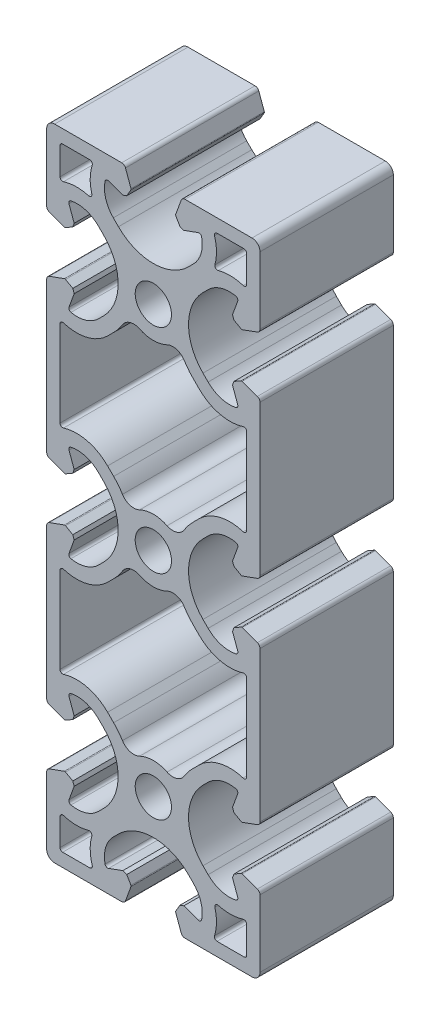
SolidWorks part; units mm, degrees
material "6005-T5"
ref_plane "Front" through (0, 0, 0) normal (0, 0, 1) x (1, 0, 0)
ref_plane "Top" through (0, 0, 0) normal (0, 1, 0) x (1, 0, 0)
ref_plane "Right" through (0, 0, 0) normal (1, 0, 0) x (0, 0, -1)
sketch "Sk Main Extrusion" plane through (0, 0, 0) normal (0, 0, 1) x (1, 0, 0)
  line L124 (17.5, 51.9407) -> (17.5, 57)
  line L125 (17, 57.5) -> (11.9407, 57.5)
  line L126 (-17.5, 57) -> (-17.5, 51.9407)
  line L127 (-11.9407, 57.5) -> (-17, 57.5)
  line L128 (-17.5, -51.9407) -> (-17.5, -57)
  line L129 (-17, -57.5) -> (-11.9407, -57.5)
  line L130 (11.9407, -57.5) -> (17, -57.5)
  line L131 (17.5, -57) -> (17.5, -51.9407)
  line L132 (17.5, 11.9407) -> (17.5, 28.0593)
  line L133 (8.5773, 30.5557) -> (7.4415, 31.6915)
  line L134 (-7.4415, 31.6915) -> (-8.5773, 30.5557)
  line L135 (-17.5, 28.0593) -> (-17.5, 11.9407)
  line L136 (-8.5773, 9.4443) -> (-7.4415, 8.3085)
  line L137 (7.4415, 8.3085) -> (8.5773, 9.4443)
  line L138 (-7.4415, -8.3085) -> (-8.5773, -9.4443)
  line L139 (-17.5, -11.9407) -> (-17.5, -28.0593)
  line L140 (-8.5773, -30.5557) -> (-7.4415, -31.6915)
  line L141 (7.4415, -31.6915) -> (8.5773, -30.5557)
  line L142 (17.5, -28.0593) -> (17.5, -11.9407)
  line L143 (8.5773, -9.4443) -> (7.4415, -8.3085)
  line L144 (4.1901, -56.6712) -> (5.2221, -59.5065)
  line L145 (5.9268, -60) -> (18.5, -60)
  line L146 (20, -58.5) -> (20, -45.9268)
  line L147 (19.5065, -45.2221) -> (16.6712, -44.1901)
  line L148 (16.4607, -44.2085) -> (15.1113, -44.9876)
  line L149 (15.1113, -44.9876) -> (14.8453, -45.7185)
  line L150 (14.8453, -45.7185) -> (15.8198, -48.3962)
  line L151 (10.2727, -47.5042) -> (9.3093, -46.5407)
  line L152 (9.3093, -33.4593) -> (10.2727, -32.4958)
  line L153 (15.8198, -31.6038) -> (14.8453, -34.2815)
  line L154 (14.8453, -34.2815) -> (15.1113, -35.0124)
  line L155 (15.1113, -35.0124) -> (16.4607, -35.7915)
  line L156 (16.6712, -35.8099) -> (19.5065, -34.7779)
  line L157 (20, -34.0732) -> (20, -5.9268)
  line L158 (19.5065, -5.2221) -> (16.6712, -4.1901)
  line L159 (16.4607, -4.2085) -> (15.1113, -4.9876)
  line L160 (15.1113, -4.9876) -> (14.8453, -5.7185)
  line L161 (14.8453, -5.7185) -> (15.8198, -8.3962)
  line L162 (10.2727, -7.5042) -> (9.3093, -6.5407)
  line L163 (9.3093, 6.5407) -> (10.2727, 7.5042)
  line L164 (15.8198, 8.3962) -> (14.8453, 5.7185)
  line L165 (14.8453, 5.7185) -> (15.1113, 4.9876)
  line L166 (15.1113, 4.9876) -> (16.4607, 4.2085)
  line L167 (16.6712, 4.1901) -> (19.5065, 5.2221)
  line L168 (20, 5.9268) -> (20, 34.0732)
  line L169 (19.5065, 34.7779) -> (16.6712, 35.8099)
  line L170 (16.4607, 35.7915) -> (15.1113, 35.0124)
  line L171 (15.1113, 35.0124) -> (14.8453, 34.2815)
  line L172 (14.8453, 34.2815) -> (15.8198, 31.6038)
  line L173 (10.2727, 32.4958) -> (9.3093, 33.4593)
  line L174 (9.3093, 46.5407) -> (10.2727, 47.5042)
  line L175 (15.8198, 48.3962) -> (14.8453, 45.7185)
  line L176 (14.8453, 45.7185) -> (15.1113, 44.9876)
  line L177 (15.1113, 44.9876) -> (16.4607, 44.2085)
  line L178 (16.6712, 44.1901) -> (19.5065, 45.2221)
  line L179 (20, 45.9268) -> (20, 58.5)
  line L180 (18.5, 60) -> (5.9268, 60)
  line L181 (5.2221, 59.5065) -> (4.1901, 56.6712)
  line L182 (4.2085, 56.4607) -> (4.9876, 55.1113)
  line L183 (4.9876, 55.1113) -> (5.7185, 54.8453)
  line L184 (5.7185, 54.8453) -> (8.3962, 55.8198)
  line L185 (7.5042, 50.2727) -> (6.5407, 49.3093)
  line L186 (-6.5407, 49.3093) -> (-7.5042, 50.2727)
  line L187 (-8.3962, 55.8198) -> (-5.7185, 54.8453)
  line L188 (-5.7185, 54.8453) -> (-4.9876, 55.1113)
  line L189 (-4.9876, 55.1113) -> (-4.2085, 56.4607)
  line L190 (-4.1901, 56.6712) -> (-5.2221, 59.5065)
  line L191 (-5.9268, 60) -> (-18.5, 60)
  line L192 (-20, 58.5) -> (-20, 45.9268)
  line L193 (-19.5065, 45.2221) -> (-16.6712, 44.1901)
  line L194 (-16.4607, 44.2085) -> (-15.1113, 44.9876)
  line L195 (-15.1113, 44.9876) -> (-14.8453, 45.7185)
  line L196 (-14.8453, 45.7185) -> (-15.8198, 48.3962)
  line L197 (-10.2727, 47.5042) -> (-9.3093, 46.5407)
  line L198 (-9.3093, 33.4593) -> (-10.2727, 32.4958)
  line L199 (-15.8198, 31.6038) -> (-14.8453, 34.2815)
  line L200 (-14.8453, 34.2815) -> (-15.1113, 35.0124)
  line L201 (-15.1113, 35.0124) -> (-16.4607, 35.7915)
  line L202 (-16.6712, 35.8099) -> (-19.5065, 34.7779)
  line L203 (-20, 34.0732) -> (-20, 5.9268)
  line L204 (-19.5065, 5.2221) -> (-16.6712, 4.1901)
  line L205 (-16.4607, 4.2085) -> (-15.1113, 4.9876)
  line L206 (-15.1113, 4.9876) -> (-14.8453, 5.7185)
  line L207 (-14.8453, 5.7185) -> (-15.8198, 8.3962)
  line L208 (-10.2727, 7.5042) -> (-9.3093, 6.5407)
  line L209 (-9.3093, -6.5407) -> (-10.2727, -7.5042)
  line L210 (-15.8198, -8.3962) -> (-14.8453, -5.7185)
  line L211 (-14.8453, -5.7185) -> (-15.1113, -4.9876)
  line L212 (-15.1113, -4.9876) -> (-16.4607, -4.2085)
  line L213 (-16.6712, -4.1901) -> (-19.5065, -5.2221)
  line L214 (-20, -5.9268) -> (-20, -34.0732)
  line L215 (-19.5065, -34.7779) -> (-16.6712, -35.8099)
  line L216 (-16.4607, -35.7915) -> (-15.1113, -35.0124)
  line L217 (-15.1113, -35.0124) -> (-14.8453, -34.2815)
  line L218 (-14.8453, -34.2815) -> (-15.8198, -31.6038)
  line L219 (-10.2727, -32.4958) -> (-9.3093, -33.4593)
  line L220 (-9.3093, -46.5407) -> (-10.2727, -47.5042)
  line L221 (-15.8198, -48.3962) -> (-14.8453, -45.7185)
  line L222 (-14.8453, -45.7185) -> (-15.1113, -44.9876)
  line L223 (-15.1113, -44.9876) -> (-16.4607, -44.2085)
  line L224 (-16.6712, -44.1901) -> (-19.5065, -45.2221)
  line L225 (-20, -45.9268) -> (-20, -58.5)
  line L226 (-18.5, -60) -> (-5.9268, -60)
  line L227 (-5.2221, -59.5065) -> (-4.1901, -56.6712)
  line L228 (-4.2085, -56.4607) -> (-4.9876, -55.1113)
  line L229 (-4.9876, -55.1113) -> (-5.7185, -54.8453)
  line L230 (-5.7185, -54.8453) -> (-8.3962, -55.8198)
  line L231 (-7.5042, -50.2727) -> (-6.5407, -49.3093)
  line L232 (6.5407, -49.3093) -> (7.5042, -50.2727)
  line L233 (8.3962, -55.8198) -> (5.7185, -54.8453)
  line L234 (5.7185, -54.8453) -> (4.9876, -55.1113)
  line L235 (4.9876, -55.1113) -> (4.2085, -56.4607)
  circle A139 centre (0, -40) radius 3.4
  circle A140 centre (0, 0) radius 3.4
  circle A141 centre (0, 40) radius 3.4
  arc A142 (11.9407, 57.5) -> (11.464, 56.8492) centre (11.9407, 57) ccw
  arc A143 (11.5401, 52.1568) -> (11.464, 56.8492) centre (3.646, 54.3755) ccw
  arc A144 (11.5401, 52.1568) -> (12.1568, 51.5401) centre (12.0215, 52.0215) ccw
  arc A145 (16.8492, 51.464) -> (12.1568, 51.5401) centre (14.3755, 43.646) ccw
  arc A146 (16.8492, 51.464) -> (17.5, 51.9407) centre (17, 51.9407) ccw
  arc A147 (17.5, 57) -> (17, 57.5) centre (17, 57) ccw
  arc A148 (-17, 57.5) -> (-17.5, 57) centre (-17, 57) ccw
  arc A149 (-17.5, 51.9407) -> (-16.8492, 51.464) centre (-17, 51.9407) ccw
  arc A150 (-12.1568, 51.5401) -> (-16.8492, 51.464) centre (-14.3755, 43.646) ccw
  arc A151 (-12.1568, 51.5401) -> (-11.5401, 52.1568) centre (-12.0215, 52.0215) ccw
  arc A152 (-11.464, 56.8492) -> (-11.5401, 52.1568) centre (-3.646, 54.3755) ccw
  arc A153 (-11.464, 56.8492) -> (-11.9407, 57.5) centre (-11.9407, 57) ccw
  arc A154 (-16.8492, -51.464) -> (-17.5, -51.9407) centre (-17, -51.9407) ccw
  arc A155 (-17.5, -57) -> (-17, -57.5) centre (-17, -57) ccw
  arc A156 (-11.9407, -57.5) -> (-11.464, -56.8492) centre (-11.9407, -57) ccw
  arc A157 (-11.5401, -52.1568) -> (-11.464, -56.8492) centre (-3.646, -54.3755) ccw
  arc A158 (-11.5401, -52.1568) -> (-12.1568, -51.5401) centre (-12.0215, -52.0215) ccw
  arc A159 (-16.8492, -51.464) -> (-12.1568, -51.5401) centre (-14.3755, -43.646) ccw
  arc A160 (12.1568, -51.5401) -> (11.5401, -52.1568) centre (12.0215, -52.0215) ccw
  arc A161 (11.464, -56.8492) -> (11.5401, -52.1568) centre (3.646, -54.3755) ccw
  arc A162 (11.464, -56.8492) -> (11.9407, -57.5) centre (11.9407, -57) ccw
  arc A163 (17, -57.5) -> (17.5, -57) centre (17, -57) ccw
  arc A164 (17.5, -51.9407) -> (16.8492, -51.464) centre (17, -51.9407) ccw
  arc A165 (12.1568, -51.5401) -> (16.8492, -51.464) centre (14.3755, -43.646) ccw
  arc A166 (16.8492, 11.464) -> (8.5773, 9.4443) centre (14.3755, 3.646) ccw
  arc A167 (16.8492, 11.464) -> (17.5, 11.9407) centre (17, 11.9407) ccw
  arc A168 (17.5, 28.0593) -> (16.8492, 28.536) centre (17, 28.0593) ccw
  arc A169 (8.5773, 30.5557) -> (16.8492, 28.536) centre (14.3755, 36.354) ccw
  arc A170 (5.2221, -59.5065) -> (5.9268, -60) centre (5.9268, -59.25) ccw
  arc A171 (18.5, -60) -> (20, -58.5) centre (18.5, -58.5) ccw
  arc A172 (20, -45.9268) -> (19.5065, -45.2221) centre (19.25, -45.9268) ccw
  arc A173 (16.6712, -44.1901) -> (16.4607, -44.2085) centre (16.5857, -44.425) ccw
  arc A174 (15.4507, -49.057) -> (15.8198, -48.3962) centre (15.35, -48.5672) ccw
  arc A175 (10.2727, -47.5042) -> (15.4507, -49.057) centre (14.3032, -43.4737) ccw
  arc A176 (9.3093, -33.4593) -> (9.3093, -46.5407) centre (15.85, -40) ccw
  arc A177 (15.4507, -30.943) -> (10.2727, -32.4958) centre (14.3032, -36.5263) ccw
  arc A178 (15.8198, -31.6038) -> (15.4507, -30.943) centre (15.35, -31.4328) ccw
  arc A179 (16.4607, -35.7915) -> (16.6712, -35.8099) centre (16.5857, -35.575) ccw
  arc A180 (19.5065, -34.7779) -> (20, -34.0732) centre (19.25, -34.0732) ccw
  arc A181 (20, -5.9268) -> (19.5065, -5.2221) centre (19.25, -5.9268) ccw
  arc A182 (16.6712, -4.1901) -> (16.4607, -4.2085) centre (16.5857, -4.425) ccw
  arc A183 (15.4507, -9.057) -> (15.8198, -8.3962) centre (15.35, -8.5672) ccw
  arc A184 (10.2727, -7.5042) -> (15.4507, -9.057) centre (14.3032, -3.4737) ccw
  arc A185 (9.3093, 6.5407) -> (9.3093, -6.5407) centre (15.85, 0) ccw
  arc A186 (15.4507, 9.057) -> (10.2727, 7.5042) centre (14.3032, 3.4737) ccw
  arc A187 (15.8198, 8.3962) -> (15.4507, 9.057) centre (15.35, 8.5672) ccw
  arc A188 (16.4607, 4.2085) -> (16.6712, 4.1901) centre (16.5857, 4.425) ccw
  arc A189 (19.5065, 5.2221) -> (20, 5.9268) centre (19.25, 5.9268) ccw
  arc A190 (20, 34.0732) -> (19.5065, 34.7779) centre (19.25, 34.0732) ccw
  arc A191 (16.6712, 35.8099) -> (16.4607, 35.7915) centre (16.5857, 35.575) ccw
  arc A192 (15.4507, 30.943) -> (15.8198, 31.6038) centre (15.35, 31.4328) ccw
  arc A193 (10.2727, 32.4958) -> (15.4507, 30.943) centre (14.3032, 36.5263) ccw
  arc A194 (9.3093, 46.5407) -> (9.3093, 33.4593) centre (15.85, 40) ccw
  arc A195 (15.4507, 49.057) -> (10.2727, 47.5042) centre (14.3032, 43.4737) ccw
  arc A196 (15.8198, 48.3962) -> (15.4507, 49.057) centre (15.35, 48.5672) ccw
  arc A197 (16.4607, 44.2085) -> (16.6712, 44.1901) centre (16.5857, 44.425) ccw
  arc A198 (19.5065, 45.2221) -> (20, 45.9268) centre (19.25, 45.9268) ccw
  arc A199 (20, 58.5) -> (18.5, 60) centre (18.5, 58.5) ccw
  arc A200 (5.9268, 60) -> (5.2221, 59.5065) centre (5.9268, 59.25) ccw
  arc A201 (4.1901, 56.6712) -> (4.2085, 56.4607) centre (4.425, 56.5857) ccw
  arc A202 (9.057, 55.4507) -> (8.3962, 55.8198) centre (8.5672, 55.35) ccw
  arc A203 (7.5042, 50.2727) -> (9.057, 55.4507) centre (3.4737, 54.3032) ccw
  arc A204 (-6.5407, 49.3093) -> (6.5407, 49.3093) centre (0, 55.85) ccw
  arc A205 (-9.057, 55.4507) -> (-7.5042, 50.2727) centre (-3.4737, 54.3032) ccw
  arc A206 (-8.3962, 55.8198) -> (-9.057, 55.4507) centre (-8.5672, 55.35) ccw
  arc A207 (-4.2085, 56.4607) -> (-4.1901, 56.6712) centre (-4.425, 56.5857) ccw
  arc A208 (-5.2221, 59.5065) -> (-5.9268, 60) centre (-5.9268, 59.25) ccw
  arc A209 (-18.5, 60) -> (-20, 58.5) centre (-18.5, 58.5) ccw
  arc A210 (-20, 45.9268) -> (-19.5065, 45.2221) centre (-19.25, 45.9268) ccw
  arc A211 (-16.6712, 44.1901) -> (-16.4607, 44.2085) centre (-16.5857, 44.425) ccw
  arc A212 (-15.4507, 49.057) -> (-15.8198, 48.3962) centre (-15.35, 48.5672) ccw
  arc A213 (-10.2727, 47.5042) -> (-15.4507, 49.057) centre (-14.3032, 43.4737) ccw
  arc A214 (-9.3093, 33.4593) -> (-9.3093, 46.5407) centre (-15.85, 40) ccw
  arc A215 (-15.4507, 30.943) -> (-10.2727, 32.4958) centre (-14.3032, 36.5263) ccw
  arc A216 (-15.8198, 31.6038) -> (-15.4507, 30.943) centre (-15.35, 31.4328) ccw
  arc A217 (-16.4607, 35.7915) -> (-16.6712, 35.8099) centre (-16.5857, 35.575) ccw
  arc A218 (-19.5065, 34.7779) -> (-20, 34.0732) centre (-19.25, 34.0732) ccw
  arc A219 (-20, 5.9268) -> (-19.5065, 5.2221) centre (-19.25, 5.9268) ccw
  arc A220 (-16.6712, 4.1901) -> (-16.4607, 4.2085) centre (-16.5857, 4.425) ccw
  arc A221 (-15.4507, 9.057) -> (-15.8198, 8.3962) centre (-15.35, 8.5672) ccw
  arc A222 (-10.2727, 7.5042) -> (-15.4507, 9.057) centre (-14.3032, 3.4737) ccw
  arc A223 (-9.3093, -6.5407) -> (-9.3093, 6.5407) centre (-15.85, 0) ccw
  arc A224 (-15.4507, -9.057) -> (-10.2727, -7.5042) centre (-14.3032, -3.4737) ccw
  arc A225 (-15.8198, -8.3962) -> (-15.4507, -9.057) centre (-15.35, -8.5672) ccw
  arc A226 (-16.4607, -4.2085) -> (-16.6712, -4.1901) centre (-16.5857, -4.425) ccw
  arc A227 (-19.5065, -5.2221) -> (-20, -5.9268) centre (-19.25, -5.9268) ccw
  arc A228 (-20, -34.0732) -> (-19.5065, -34.7779) centre (-19.25, -34.0732) ccw
  arc A229 (-16.6712, -35.8099) -> (-16.4607, -35.7915) centre (-16.5857, -35.575) ccw
  arc A230 (-15.4507, -30.943) -> (-15.8198, -31.6038) centre (-15.35, -31.4328) ccw
  arc A231 (-10.2727, -32.4958) -> (-15.4507, -30.943) centre (-14.3032, -36.5263) ccw
  arc A232 (-9.3093, -46.5407) -> (-9.3093, -33.4593) centre (-15.85, -40) ccw
  arc A233 (-15.4507, -49.057) -> (-10.2727, -47.5042) centre (-14.3032, -43.4737) ccw
  arc A234 (-15.8198, -48.3962) -> (-15.4507, -49.057) centre (-15.35, -48.5672) ccw
  arc A235 (-16.4607, -44.2085) -> (-16.6712, -44.1901) centre (-16.5857, -44.425) ccw
  arc A236 (-19.5065, -45.2221) -> (-20, -45.9268) centre (-19.25, -45.9268) ccw
  arc A237 (-20, -58.5) -> (-18.5, -60) centre (-18.5, -58.5) ccw
  arc A238 (-5.9268, -60) -> (-5.2221, -59.5065) centre (-5.9268, -59.25) ccw
  arc A239 (-4.1901, -56.6712) -> (-4.2085, -56.4607) centre (-4.425, -56.5857) ccw
  arc A240 (-9.057, -55.4507) -> (-8.3962, -55.8198) centre (-8.5672, -55.35) ccw
  arc A241 (-7.5042, -50.2727) -> (-9.057, -55.4507) centre (-3.4737, -54.3032) ccw
  arc A242 (6.5407, -49.3093) -> (-6.5407, -49.3093) centre (0, -55.85) ccw
  arc A243 (9.057, -55.4507) -> (7.5042, -50.2727) centre (3.4737, -54.3032) ccw
  arc A244 (8.3962, -55.8198) -> (9.057, -55.4507) centre (8.5672, -55.35) ccw
  arc A245 (4.2085, -56.4607) -> (4.1901, -56.6712) centre (4.425, -56.5857) ccw
  arc A246 (5.7881, 33.7692) -> (7.4415, 31.6915) centre (15.75, 40) ccw
  arc A247 (5.7881, 33.7692) -> (2.5767, 34.6924) centre (3.6686, 32.4434) ccw
  arc A248 (-2.5767, 34.6924) -> (2.5767, 34.6924) centre (0, 40) ccw
  arc A249 (-2.5767, 34.6924) -> (-5.7881, 33.7692) centre (-3.6686, 32.4434) ccw
  arc A250 (-7.4415, 31.6915) -> (-5.7881, 33.7692) centre (-15.75, 40) ccw
  arc A251 (-16.8492, 28.536) -> (-8.5773, 30.5557) centre (-14.3755, 36.354) ccw
  arc A252 (-16.8492, 28.536) -> (-17.5, 28.0593) centre (-17, 28.0593) ccw
  arc A253 (-17.5, 11.9407) -> (-16.8492, 11.464) centre (-17, 11.9407) ccw
  arc A254 (-8.5773, 9.4443) -> (-16.8492, 11.464) centre (-14.3755, 3.646) ccw
  arc A255 (-5.7881, 6.2308) -> (-7.4415, 8.3085) centre (-15.75, 0) ccw
  arc A256 (-5.7881, 6.2308) -> (-2.5767, 5.3076) centre (-3.6686, 7.5566) ccw
  arc A257 (2.5767, 5.3076) -> (-2.5767, 5.3076) centre (0, 0) ccw
  arc A258 (2.5767, 5.3076) -> (5.7881, 6.2308) centre (3.6686, 7.5566) ccw
  arc A259 (7.4415, 8.3085) -> (5.7881, 6.2308) centre (15.75, 0) ccw
  arc A260 (5.7881, -6.2308) -> (2.5767, -5.3076) centre (3.6686, -7.5566) ccw
  arc A261 (-2.5767, -5.3076) -> (2.5767, -5.3076) centre (0, 0) ccw
  arc A262 (-2.5767, -5.3076) -> (-5.7881, -6.2308) centre (-3.6686, -7.5566) ccw
  arc A263 (-7.4415, -8.3085) -> (-5.7881, -6.2308) centre (-15.75, 0) ccw
  arc A264 (-16.8492, -11.464) -> (-8.5773, -9.4443) centre (-14.3755, -3.646) ccw
  arc A265 (-16.8492, -11.464) -> (-17.5, -11.9407) centre (-17, -11.9407) ccw
  arc A266 (-17.5, -28.0593) -> (-16.8492, -28.536) centre (-17, -28.0593) ccw
  arc A267 (-8.5773, -30.5557) -> (-16.8492, -28.536) centre (-14.3755, -36.354) ccw
  arc A268 (-5.7881, -33.7692) -> (-7.4415, -31.6915) centre (-15.75, -40) ccw
  arc A269 (-5.7881, -33.7692) -> (-2.5767, -34.6924) centre (-3.6686, -32.4434) ccw
  arc A270 (2.5767, -34.6924) -> (-2.5767, -34.6924) centre (0, -40) ccw
  arc A271 (2.5767, -34.6924) -> (5.7881, -33.7692) centre (3.6686, -32.4434) ccw
  arc A272 (7.4415, -31.6915) -> (5.7881, -33.7692) centre (15.75, -40) ccw
  arc A273 (16.8492, -28.536) -> (8.5773, -30.5557) centre (14.3755, -36.354) ccw
  arc A274 (16.8492, -28.536) -> (17.5, -28.0593) centre (17, -28.0593) ccw
  arc A275 (17.5, -11.9407) -> (16.8492, -11.464) centre (17, -11.9407) ccw
  arc A276 (8.5773, -9.4443) -> (16.8492, -11.464) centre (14.3755, -3.646) ccw
  arc A277 (5.7881, -6.2308) -> (7.4415, -8.3085) centre (15.75, 0) ccw
extrude "Main Extrusion" add sketch "Sk Main Extrusion" against normal blind 25
sketch "Threaded Insert Mate Sketch" plane through (0, 0, 0) normal (0, 0, 1) x (1, 0, 0)
  line L0 (-17.5, 20) -> (17.5, 20) construction
  line L3 (-12.7, 0) -> (12.7, 0) construction
  line L4 (-17.5, 28.0593) -> (-17.5, 11.9407) construction
  line L5 (17.5, 11.9407) -> (17.5, 28.0593) construction
  circle A0 centre (0, 52.7) radius 5.6515
  circle A2 centre (12.7, 40) radius 5.6515
  circle A3 centre (0, 27.3) radius 5.6515
  circle A4 centre (-12.7, 40) radius 5.6515
  circle A6 centre (12.7, 0) radius 5.6515
  circle A7 centre (-12.7, 0) radius 5.6515
  circle A8 centre (-12.7, -40) radius 5.6515
  circle A9 centre (0, -52.7) radius 5.6515
  circle A10 centre (12.7, -40) radius 5.6515
  circle A11 centre (0, 40) radius 3.4 construction
  point P14 (0, 40)
  dimension "D2" = 11.303
  dimension "D1" = 12.7
  dimension "D3" = 4
equation "\"Weight kg\"= round ( \"SW-Mass\" , 2 )"
equation "\"Weight lbs\"= round ( \"SW-Mass\" * 2.2046 , 2 )"
equation "\"Length mm\"= round ( \"Length@Main Extrusion\" , 2 )"
equation "\"Length in\"= round ( \"Length@Main Extrusion\" / 25.4 , 3 )"
